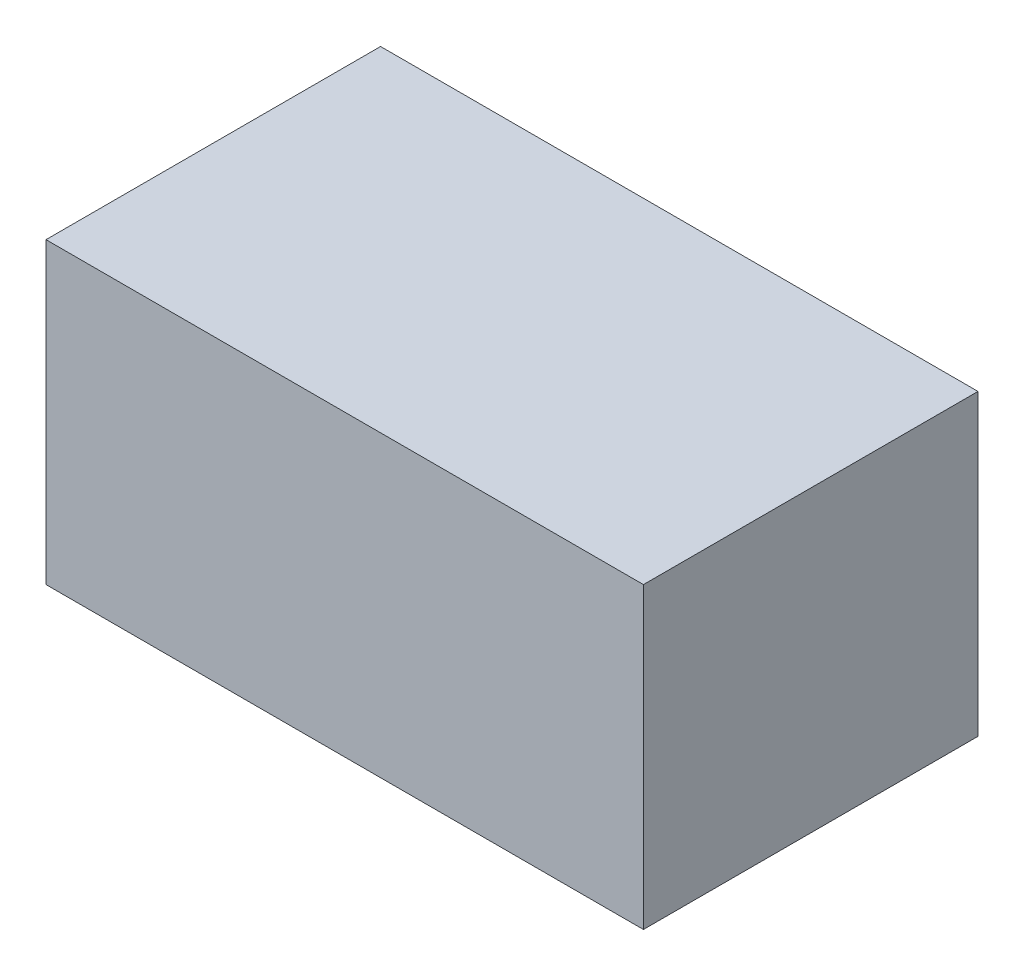
SolidWorks part; units mm, degrees
ref_plane "Front Plane" through (0, 0, 0) normal (0, 0, 1) x (1, 0, 0)
ref_plane "Top Plane" through (0, 0, 0) normal (0, 1, 0) x (1, 0, 0)
ref_plane "Right Plane" through (0, 0, 0) normal (1, 0, 0) x (0, 0, -1)
sketch "Sketch1" plane through (0, 0, 0) normal (0, 0, 1) x (1, 0, 0)
  line L1 (0, 0) -> (50, 0)
  line L2 (0, 0) -> (0, -25)
  line L3 (0, -25) -> (50, -25)
  line L4 (50, 0) -> (50, -25)
  dimension "D1" = 50
  dimension "D2" = 25
extrude "Boss-Extrude1" add sketch "Sketch1" along normal blind 28
